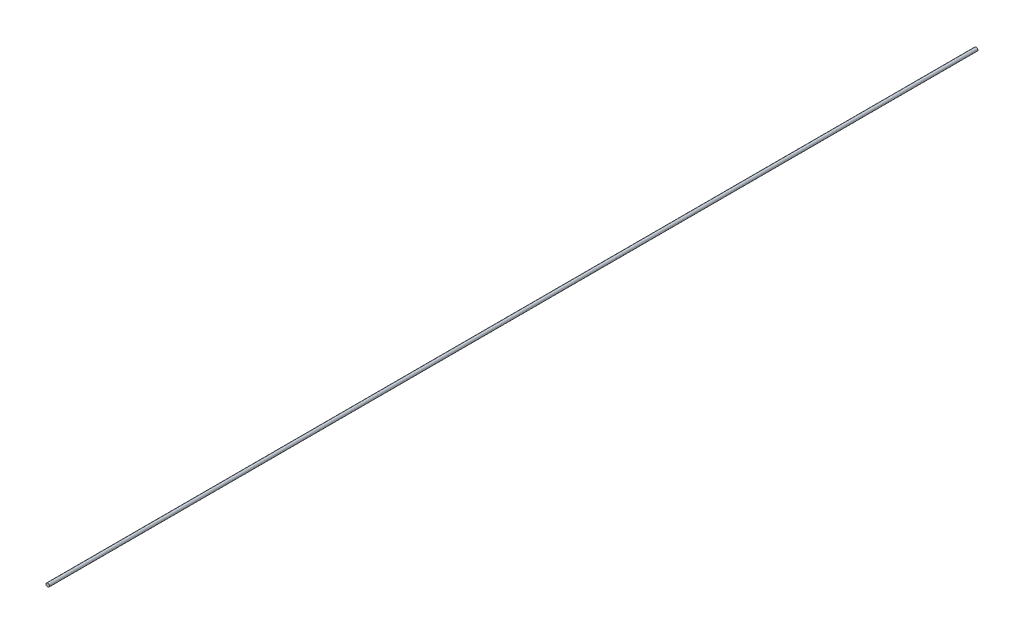
SolidWorks part; units mm, degrees
ref_plane "Front Plane" through (0, 0, 0) normal (0, 0, 1) x (1, 0, 0)
ref_plane "Top Plane" through (0, 0, 0) normal (0, 1, 0) x (1, 0, 0)
ref_plane "Right Plane" through (0, 0, 0) normal (1, 0, 0) x (0, 0, -1)
sketch "Sketch1" plane through (0, 0, 0) normal (0, 0, 1) x (1, 0, 0)
  circle A0 centre (0, 0) radius 3.8
  dimension "D1" = 7.6
extrude "Boss-Extrude1" add sketch "Sketch1" along normal blind 2072
